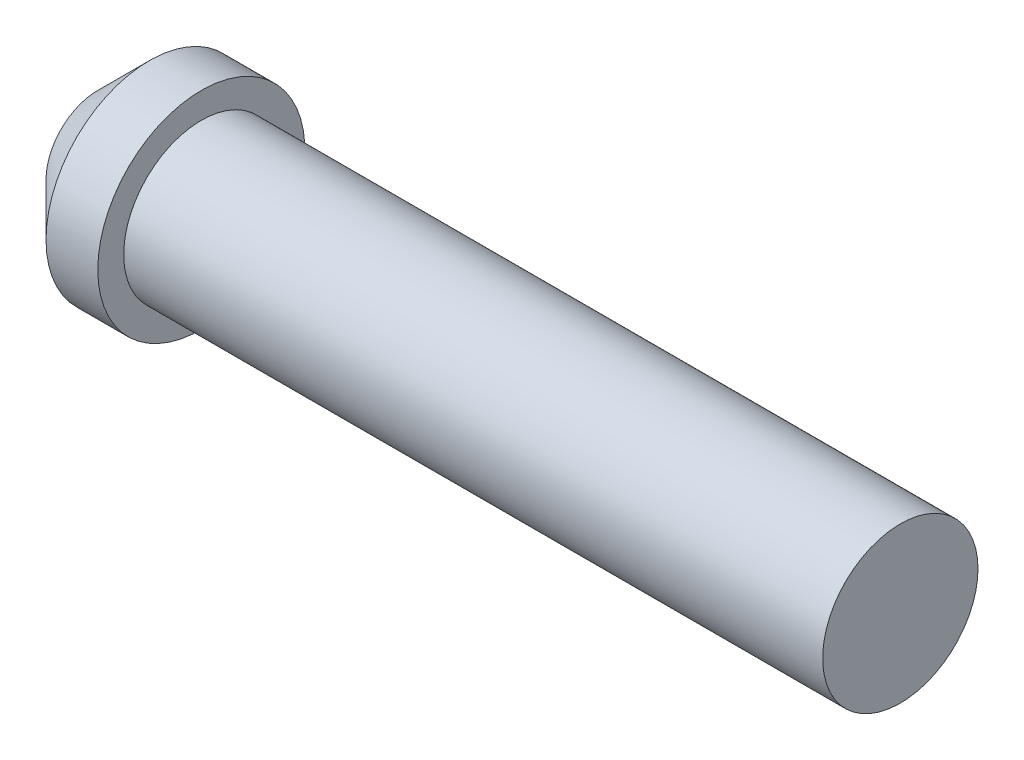
SolidWorks part; units mm, degrees
ref_plane "Front Plane" through (0, 0, 0) normal (0, 0, 1) x (1, 0, 0)
ref_plane "Top Plane" through (0, 0, 0) normal (0, 1, 0) x (1, 0, 0)
ref_plane "Right Plane" through (0, 0, 0) normal (1, 0, 0) x (0, 0, -1)
sketch "Sketch1" plane through (0, 0, 0) normal (1, 0, 0) x (0, 0, -1)
  circle A0 centre (0, 0) radius 3
  dimension "D1" = 6
extrude "Boss-Extrude1" add sketch "Sketch1" along normal blind 27
sketch "Sketch2" plane through (0, 0, 0) normal (-1, 0, 0) x (0, 0, 1)
  circle A0 centre (0, 0) radius 4
  dimension "D1" = 8
extrude "Boss-Extrude2" add sketch "Sketch2" along normal blind 4
chamfer "Chamfer1" distance 2 angle 45 1 edges at (-4, 0, 4)
